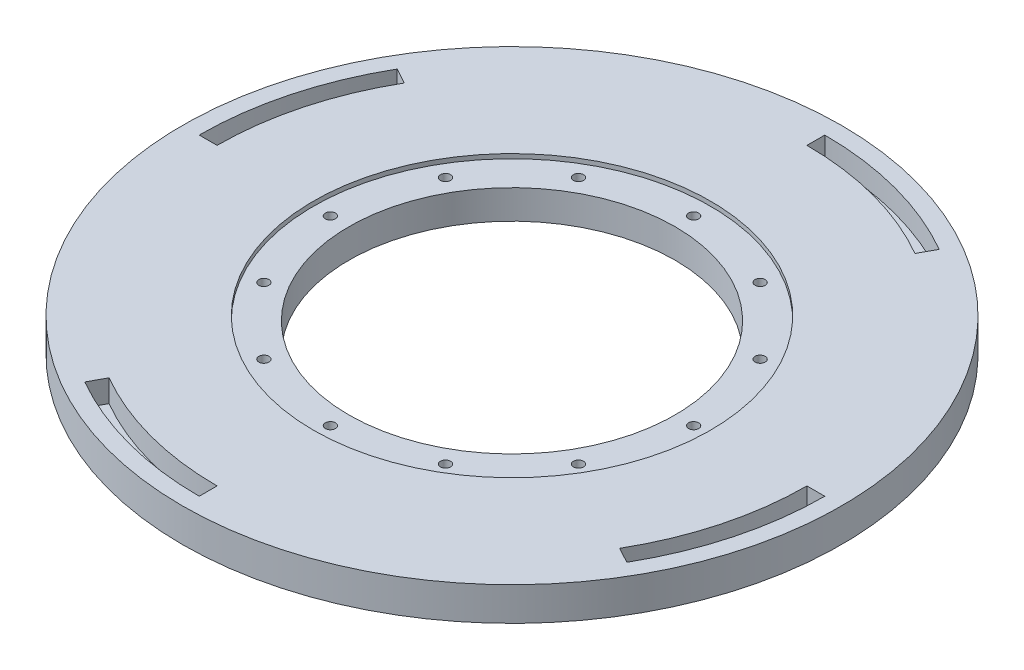
SolidWorks part; units mm, degrees
material "6061-T6 (SS)"
ref_plane "Front Plane" through (0, 0, 0) normal (0, 0, 1) x (1, 0, 0)
ref_plane "Top Plane" through (0, 0, 0) normal (0, 1, 0) x (1, 0, 0)
ref_plane "Right Plane" through (0, 0, 0) normal (1, 0, 0) x (0, 0, -1)
sketch "Sketch1" plane through (0, 0, 0) normal (0, 1, 0) x (1, 0, 0)
  line L5 (0, 0) -> (127.635, 0)
  line L6 (0, 0) -> (0, 127.635)
  line L7 (0, 127.635) -> (127.635, 127.635)
  line L8 (127.635, 0) -> (127.635, 127.635)
  dimension "D1" = 127.635
  dimension "D2" = 127.635
extrude "Boss-Extrude1" add sketch "Sketch1" along normal blind 9.525 contours L5 L8 L7 L6
sketch "Sketch13" plane through (0, 9.525, 0) normal (0, 1, 0) x (1, 0, 0)
  circle A0 centre (63.8175, 63.8175) radius 93.6625
  dimension "D1" = 187.325
extrude "Boss-Extrude2" add sketch "Sketch13" against normal up to surface (9.525 mm away) contours A0 up to face at (63.8175, 0, -63.8175)
sketch "Sketch6" [suppressed] plane through (127.635, 0, 0) normal (1, 0, 0) x (0, 0, -1)
  circle A0 centre (4.7625, 4.7625) radius 1.3526
  dimension "D1" = 2.7051
extrude "6-32 hole1" [suppressed] cut sketch "Sketch6" against normal blind 12.7
sketch "Sketch7" [suppressed] plane through (0, 0, -127.635) normal (0, 0, -1) x (-1, 0, 0)
  circle A0 centre (-122.8725, 4.7625) radius 1.3525
  dimension "D1" = 2.7051
sketch "Sketch8" [suppressed] plane through (0, 0, 0) normal (-1, 0, 0) x (0, 0, 1)
  circle A0 centre (-122.8725, 4.7625) radius 1.3525
  dimension "D1" = 2.7051
sketch "Sketch9" [suppressed] plane through (0, 0, 0) normal (0, 0, 1) x (1, 0, 0)
  circle A0 centre (4.7625, 4.7625) radius 1.3526
  dimension "D1" = 2.7051
sketch "Sketch5" plane through (0, 9.525, 0) normal (0, 1, 0) x (1, 0, 0)
  circle A0 centre (63.8175, 63.8175) radius 46.355
  circle A1 centre (63.8175, 63.8175) radius 93.6625 construction
  dimension "D1" = 92.71
extrude "Cut-Extrude1" cut sketch "Sketch5" against normal blind 9.525
sketch "Sketch11" plane through (0, 9.525, 0) normal (0, 1, 0) x (1, 0, 0)
  line L0 (63.8175, 63.8175) -> (63.8175, 115.443) construction
  circle A0 centre (63.8175, 115.443) radius 1.4351
  dimension "D2" = 2.8702
  dimension "D1" = 51.6255
extrude "Cut-Extrude3" cut sketch "Sketch11" against normal through all contours A0
pattern_circular "CirPattern1" count 12 over 360 about axis through (63.8175, 0, -63.8175) along (0, 1, 0) of "Cut-Extrude3"
sketch "Sketch12" plane through (0, 9.525, 0) normal (0, 1, 0) x (1, 0, 0)
  circle A0 centre (63.8175, 63.8175) radius 56.4198
  dimension "D1" = 112.8395
extrude "Cut-Extrude4" cut sketch "Sketch12" against normal blind 1.27
sketch "Sketch15" plane through (0, 9.525, 0) normal (0, 1, 0) x (1, 0, 0)
  line L0 (63.8175, 63.8175) -> (-29.845, 63.8175) construction
  line L1 (0, -39.1057) -> (0, 39.1057) construction
  line L2 (-20.0025, 63.8175) -> (-25.0825, 63.8175)
  line L3 (-8.7458, 105.7742) -> (-13.2051, 108.2104)
  line L4 (-8.7458, 105.7742) -> (-20.0025, 63.8175) construction
  circle A0 centre (63.8175, 63.8175) radius 56.4198 construction
  arc A1 (-20.0025, 63.8175) -> (-8.7458, 105.7742) centre (63.8175, 63.8175) cw
  arc A2 (-25.0825, 63.8175) -> (-13.2051, 108.2104) centre (63.8175, 63.8175) cw
  circle A3 centre (63.8175, 63.8175) radius 93.6625 construction
  point P0 (63.8175, 63.8175)
  point P11 (-14.3741, 84.7959)
  point P14 (0, 0)
  point P15 (0, 0)
  point P16 (0, 0)
  point P17 (0, 0)
  point P18 (0, 0)
  dimension "D1" = 46.482
  dimension "D2" = 88.9
  dimension "D3" = 83.82
  dimension "D4" = 43.942
extrude "Support hole" cut sketch "Sketch15" against normal blind 6.35
sketch "Sketch16" plane through (0, 0, 0) normal (0, -1, 0) x (-1, 0, 0)
  line L0 (26.6457, 88.0883) -> (-63.8175, 63.8175) construction
  circle A0 centre (19.5927, 86.196) radius 1.27
  circle A1 centre (-63.8175, 63.8175) radius 93.6625 construction
  point P2 (0, 0)
  point P3 (0, 0)
  point P5 (21.2432, 88.1388)
  point P6 (0, 0)
  point P7 (0, 0)
  dimension "D1" = 2.54
  dimension "D3" = 86.36
extrude "Frame bolt hole" cut sketch "Sketch16" against normal up to surface (3.175 mm away) up to face at (-18.1798, 3.175, -85.7856)
pattern_circular "Frame support pattern" count 4 over 360 about axis through (63.8175, 0, -63.8175) along (0, 1, 0) of "Support hole", "Frame bolt hole"
